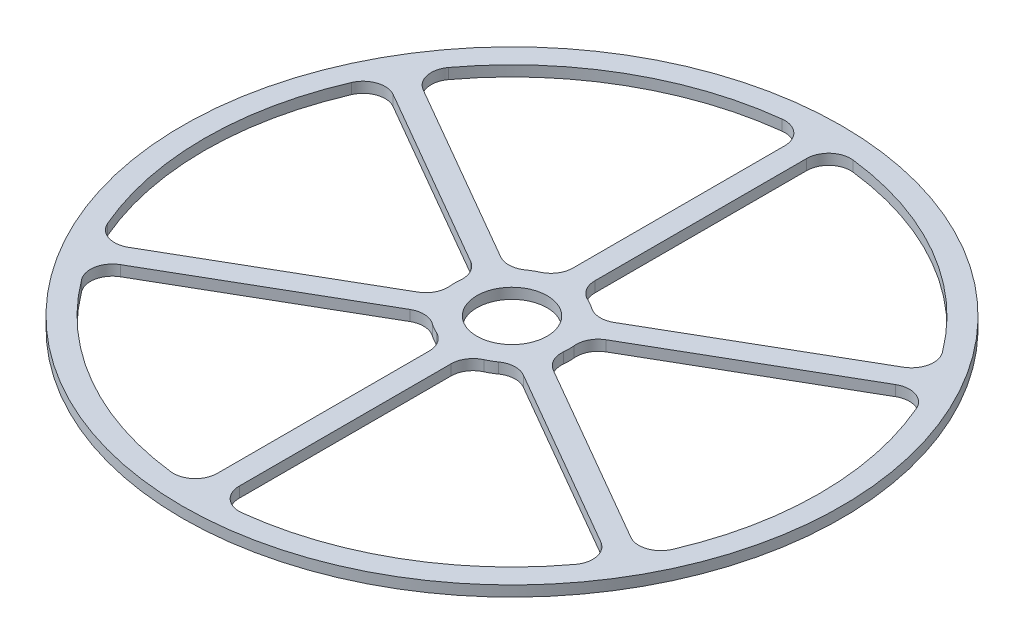
SolidWorks part; units mm, degrees
material "ABS PC"
ref_plane "Front Plane" through (0, 0, 0) normal (0, 0, 1) x (1, 0, 0)
ref_plane "Top Plane" through (0, 0, 0) normal (0, 1, 0) x (1, 0, 0)
ref_plane "Right Plane" through (0, 0, 0) normal (1, 0, 0) x (0, 0, -1)
sketch "Sketch1" plane through (0, 0, 0) normal (0, 1, 0) x (1, 0, 0)
  line L0 (0, 0) -> (0, 47.625) construction
  line L1 (0, 0) -> (41.2445, 23.8125) construction
  line L2 (1.5875, 40.9993) -> (1.5875, 10.3905)
  line L3 (8.2047, 6.5701) -> (34.7127, 21.8745)
  line L4 (36.3002, 19.1248) -> (9.7922, 3.8205)
  line L5 (9.7922, -3.8205) -> (36.3002, -19.1248)
  line L6 (34.7127, -21.8745) -> (8.2047, -6.5701)
  line L7 (1.5875, -10.3905) -> (1.5875, -40.9993)
  line L8 (-1.5875, -40.9993) -> (-1.5875, -10.3905)
  line L9 (-8.2047, -6.5701) -> (-34.7127, -21.8745)
  line L10 (-36.3002, -19.1248) -> (-9.7922, -3.8205)
  line L11 (-9.7922, 3.8205) -> (-36.3002, 19.1248)
  line L12 (-34.7127, 21.8745) -> (-8.2047, 6.5701)
  line L13 (-1.5875, 10.3905) -> (-1.5875, 40.9993)
  circle A0 centre (0, 0) radius 47.625
  circle A1 centre (0, 0) radius 5.08
  circle A2 centre (0, 0) radius 8.255 construction
  circle A3 centre (0, 0) radius 44.45 construction
  arc A4 (5.1288, 44.1531) -> (35.6733, 26.5183) centre (0, 0) cw
  arc A5 (3.4396, 7.5043) -> (4.7791, 6.7309) centre (0, 0) cw
  arc A6 (1.5875, 40.9993) -> (5.1288, 44.1531) centre (4.7625, 40.9993) cw
  arc A7 (34.7127, 21.8745) -> (35.6733, 26.5183) centre (33.1252, 24.6241) ccw
  arc A8 (8.2047, 6.5701) -> (4.7791, 6.7309) centre (6.6172, 9.3197) cw
  arc A9 (1.5875, 10.3905) -> (3.4396, 7.5043) centre (4.7625, 10.3905) ccw
  arc A10 (36.3002, 19.1248) -> (40.8021, 17.6348) centre (37.8877, 16.3752) cw
  arc A11 (40.8021, 17.6348) -> (40.8021, -17.6348) centre (0, 0) cw
  arc A12 (36.3002, -19.1248) -> (40.8021, -17.6348) centre (37.8877, -16.3752) ccw
  arc A13 (9.7922, -3.8205) -> (8.2187, -0.7734) centre (11.3797, -1.0708) cw
  arc A14 (9.7922, 3.8205) -> (8.2187, 0.7734) centre (11.3797, 1.0708) ccw
  arc A15 (34.7127, -21.8745) -> (35.6733, -26.5183) centre (33.1252, -24.6241) cw
  arc A16 (35.6733, -26.5183) -> (5.1288, -44.1531) centre (0, 0) cw
  arc A17 (1.5875, -40.9993) -> (5.1288, -44.1531) centre (4.7625, -40.9993) ccw
  arc A18 (1.5875, -10.3905) -> (3.4396, -7.5043) centre (4.7625, -10.3905) cw
  arc A19 (8.2047, -6.5701) -> (4.7791, -6.7309) centre (6.6172, -9.3197) ccw
  arc A20 (-1.5875, -40.9993) -> (-5.1288, -44.1531) centre (-4.7625, -40.9993) cw
  arc A21 (-5.1288, -44.1531) -> (-35.6733, -26.5183) centre (0, 0) cw
  arc A22 (-34.7127, -21.8745) -> (-35.6733, -26.5183) centre (-33.1252, -24.6241) ccw
  arc A23 (-8.2047, -6.5701) -> (-4.7791, -6.7309) centre (-6.6172, -9.3197) cw
  arc A24 (-1.5875, -10.3905) -> (-3.4396, -7.5043) centre (-4.7625, -10.3905) ccw
  arc A25 (-36.3002, -19.1248) -> (-40.8021, -17.6348) centre (-37.8877, -16.3752) cw
  arc A26 (-40.8021, -17.6348) -> (-40.8021, 17.6348) centre (0, 0) cw
  arc A27 (-36.3002, 19.1248) -> (-40.8021, 17.6348) centre (-37.8877, 16.3752) ccw
  arc A28 (-9.7922, 3.8205) -> (-8.2187, 0.7734) centre (-11.3797, 1.0708) cw
  arc A29 (-9.7922, -3.8205) -> (-8.2187, -0.7734) centre (-11.3797, -1.0708) ccw
  arc A30 (-34.7127, 21.8745) -> (-35.6733, 26.5183) centre (-33.1252, 24.6241) cw
  arc A31 (-35.6733, 26.5183) -> (-5.1288, 44.1531) centre (0, 0) cw
  arc A32 (-1.5875, 40.9993) -> (-5.1288, 44.1531) centre (-4.7625, 40.9993) ccw
  arc A33 (-1.5875, 10.3905) -> (-3.4396, 7.5043) centre (-4.7625, 10.3905) cw
  arc A34 (-8.2047, 6.5701) -> (-4.7791, 6.7309) centre (-6.6172, 9.3197) ccw
  arc A35 (8.2187, 0.7734) -> (8.2187, -0.7734) centre (0, 0) cw
  arc A36 (4.7791, -6.7309) -> (3.4396, -7.5043) centre (0, 0) cw
  arc A37 (-3.4396, -7.5043) -> (-4.7791, -6.7309) centre (0, 0) cw
  arc A38 (-8.2187, -0.7734) -> (-8.2187, 0.7734) centre (0, 0) cw
  arc A39 (-4.7791, 6.7309) -> (-3.4396, 7.5043) centre (0, 0) cw
  point P16 (1.5875, 44.4216)
  point P19 (37.6765, 23.5856)
  point P22 (6.2219, 5.4253)
  point P25 (1.5875, 8.1009)
  point P89 (0, 0)
  point P100 (0, 0)
  dimension "D1" = 95.25
  dimension "D2" = 10.16
  dimension "D3" = 3.175
  dimension "D4" = 3.175
  dimension "D8" = 3.175
  dimension "D5" = 60
  dimension "D6" = 3.175
  dimension "D7" = 3.175
  dimension "D9" = 6
  dimension "D10" = 6
extrude "Boss-Extrude1" add sketch "Sketch1" along normal blind 1.524
